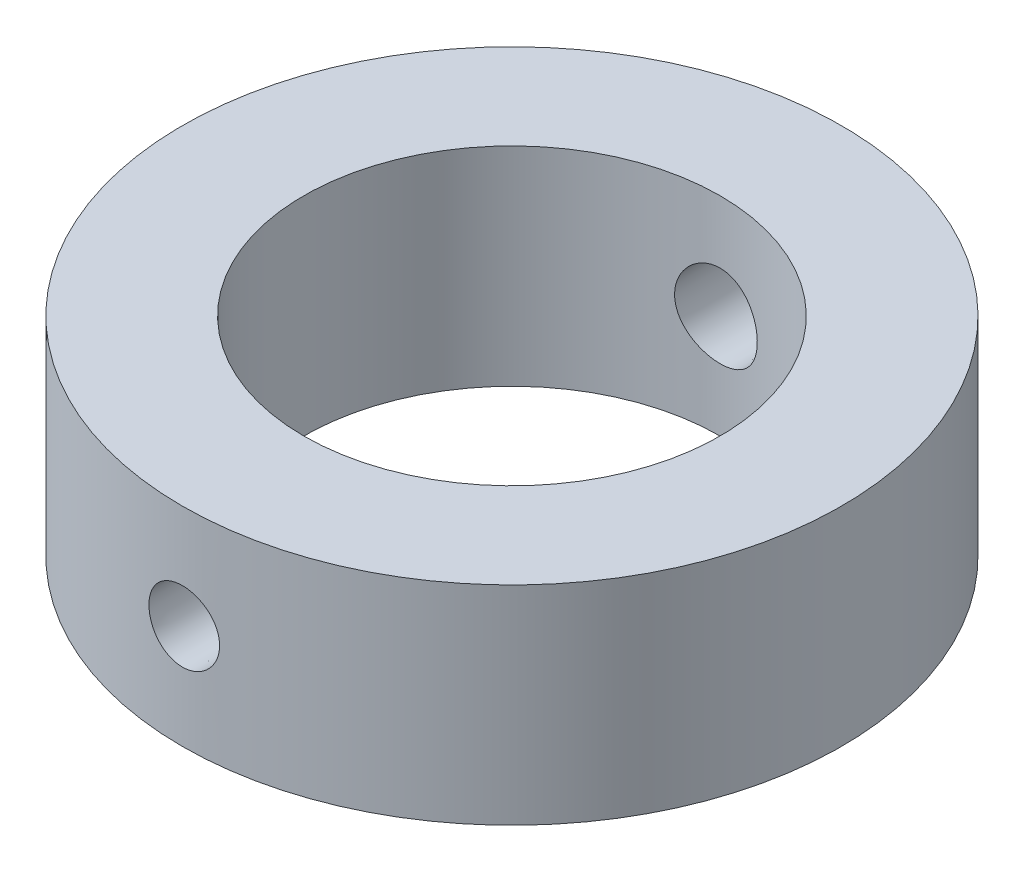
SolidWorks part; units mm, degrees
ref_plane "Front Plane" through (0, 0, 0) normal (0, 0, 1) x (1, 0, 0)
ref_plane "Top Plane" through (0, 0, 0) normal (0, 1, 0) x (1, 0, 0)
ref_plane "Right Plane" through (0, 0, 0) normal (1, 0, 0) x (0, 0, -1)
sketch "Sketch1" plane through (0, 0, 0) normal (0, 1, 0) x (1, 0, 0)
  circle A0 centre (0, 0) radius 12
  circle A1 centre (0, 0) radius 19
  dimension "D1" = 24
  dimension "D2" = 38
extrude "Boss-Extrude1" add sketch "Sketch1" along normal mid plane 12
sketch "Sketch2" plane through (0, 0, 0) normal (0, 1, 0) x (1, 0, 0)
  line L0 (0, 26.0031) -> (0, -25.7774) construction
  line L1 (0, 22) -> (0, -22)
  line L2 (0, -22) -> (2, -22)
  line L3 (2, -22) -> (2.5, 22)
  line L4 (2.5, 22) -> (0, 22)
  dimension "D1" = 44
  dimension "D2" = 22
  dimension "D3" = 2
  dimension "D4" = 2.5
revolve "Cut-Revolve1" cut sketch "Sketch2" angle 360 about L0
